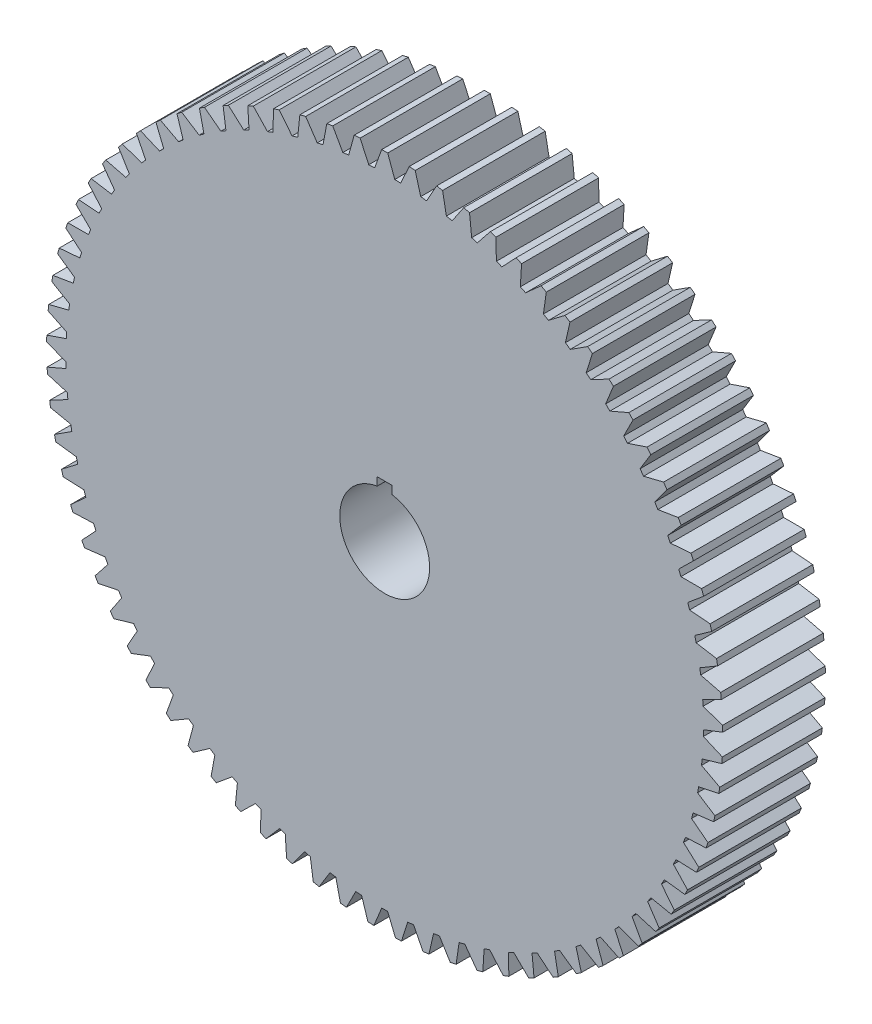
SolidWorks part; units mm, degrees
ref_plane "Front Plane" through (0, 0, 0) normal (0, 0, 1) x (1, 0, 0)
ref_plane "Top Plane" through (0, 0, 0) normal (0, 1, 0) x (1, 0, 0)
ref_plane "Right Plane" through (0, 0, 0) normal (1, 0, 0) x (0, 0, -1)
sketch "Sketch2" plane through (0, 0, 0) normal (0, 0, 1) x (1, 0, 0)
  line L0 (1.27, 143.3266) -> (4.2647, 135.0988)
  line L1 (-1.27, 143.3266) -> (-4.2647, 135.0988)
  line L2 (0, 19.05) -> (0, 143.3322) construction
  line L3 (12.9482, 142.7461) -> (15.2623, 134.3017)
  line L4 (10.4167, 142.9532) -> (6.7613, 134.9969)
  line L5 (24.5403, 141.2158) -> (26.1583, 132.6108)
  line L6 (22.034, 141.6285) -> (17.7423, 133.9966)
  line L7 (35.969, 138.7456) -> (36.8803, 130.0374)
  line L8 (33.5047, 139.3612) -> (28.6053, 132.1046)
  line L9 (47.1584, 135.3522) -> (47.3568, 126.5986)
  line L10 (44.7525, 136.1666) -> (39.2778, 129.3334)
  line L11 (58.0339, 131.0579) -> (57.5182, 122.3173)
  line L12 (55.7024, 132.0657) -> (49.689, 125.7015)
  line L13 (68.5233, 125.8915) -> (67.2968, 117.2221)
  line L14 (66.2817, 127.086) -> (59.7695, 121.2332)
  line L15 (78.5566, 119.8874) -> (76.6276, 111.3467)
  line L16 (76.4198, 121.2606) -> (69.4523, 115.958)
  line L17 (88.0671, 113.0854) -> (85.4484, 104.7303)
  line L18 (86.0494, 114.6282) -> (78.6728, 109.9112)
  line L19 (96.9916, 105.5308) -> (93.7006, 97.417)
  line L20 (95.1063, 107.233) -> (87.3698, 103.1329)
  line L21 (105.2706, 97.2739) -> (101.3292, 89.4554)
  line L22 (103.5304, 99.1241) -> (95.4854, 95.6682)
  line L23 (112.8491, 88.3697) -> (108.2835, 80.8985)
  line L24 (111.2654, 90.3556) -> (102.9655, 87.567)
  line L25 (119.6765, 78.8774) -> (114.5171, 71.8032)
  line L26 (118.26, 80.9858) -> (109.7604, 78.883)
  line L27 (125.7075, 68.8602) -> (119.9887, 62.2301)
  line L28 (124.4676, 71.077) -> (115.8249, 69.674)
  line L29 (130.902, 58.3848) -> (124.6618, 52.2428)
  line L30 (129.8469, 60.6952) -> (121.1186, 60.0013)
  line L31 (135.2253, 47.5208) -> (128.5053, 41.9079)
  line L32 (134.362, 49.9096) -> (125.6062, 49.9294)
  line L33 (138.6488, 36.3405) -> (131.4936, 31.2941)
  line L34 (137.983, 38.7917) -> (129.258, 39.5252)
  line L35 (141.1495, 24.9185) -> (133.6068, 20.472)
  line L36 (140.6858, 27.4158) -> (132.0496, 28.858)
  line L37 (142.711, 13.3305) -> (134.8309, 9.5137)
  line L38 (142.4523, 15.8573) -> (133.9624, 17.9987)
  line L39 (143.3227, 1.6539) -> (135.1577, -1.508)
  line L40 (143.2708, 4.1934) -> (134.9837, 7.0196)
  line L41 (142.9806, -10.0337) -> (134.585, -12.5195)
  line L42 (143.1359, -7.4985) -> (135.1067, -4.0062)
  line L43 (141.687, -21.6546) -> (133.1168, -23.4478)
  line L44 (142.0485, -19.1404) -> (134.3306, -15.0053)
  line L45 (139.4505, -33.1313) -> (130.7626, -34.2201)
  line L46 (140.0157, -30.655) -> (132.6606, -25.9046)
  line L47 (136.286, -44.3876) -> (127.5383, -44.7646)
  line L48 (137.0511, -41.9656) -> (130.1077, -36.6314)
  line L49 (132.2145, -55.3485) -> (123.4652, -55.0112)
  line L50 (133.1745, -52.9969) -> (126.689, -47.1145)
  line L51 (127.2631, -65.941) -> (118.5704, -64.8917)
  line L52 (128.4116, -63.6755) -> (122.4271, -57.2841)
  line L53 (121.4649, -76.0947) -> (112.8866, -74.3403)
  line L54 (122.7942, -73.9304) -> (117.3506, -67.0724)
  line L55 (114.8583, -85.742) -> (106.4516, -83.2943)
  line L56 (116.3596, -83.6932) -> (111.4931, -76.4144)
  line L57 (107.4873, -94.8187) -> (99.3081, -91.6939)
  line L58 (109.1507, -92.8991) -> (104.8936, -85.2479)
  line L59 (99.4011, -103.2645) -> (91.5038, -99.4833)
  line L60 (101.2153, -101.4868) -> (97.5961, -93.514)
  line L61 (90.6533, -111.023) -> (83.0905, -106.6107)
  line L62 (92.6064, -109.3991) -> (89.6491, -101.1579)
  line L63 (81.3023, -118.0426) -> (74.1242, -113.0286)
  line L64 (83.3812, -116.5834) -> (81.1055, -108.1285)
  line L65 (71.4102, -124.2767) -> (64.6647, -118.6944)
  line L66 (73.6012, -122.9918) -> (72.0221, -114.3796)
  line L67 (61.0428, -129.6838) -> (54.7748, -123.5702)
  line L68 (63.3313, -128.5817) -> (62.4595, -119.8695)
  line L69 (50.2693, -134.2279) -> (44.5205, -127.6237)
  line L70 (52.64, -133.316) -> (52.4812, -124.5616)
  line L71 (39.1612, -137.8786) -> (33.9698, -130.8278)
  line L72 (41.5983, -137.163) -> (42.1536, -128.4249)
  line L73 (27.7925, -140.6119) -> (23.1931, -133.1614)
  line L74 (30.2798, -140.0973) -> (31.5456, -131.4335)
  line L75 (16.2389, -142.4093) -> (12.262, -134.6088)
  line L76 (18.7599, -142.0992) -> (20.7276, -133.5674)
  line L77 (4.5771, -143.2591) -> (1.2494, -135.1603)
  line L78 (7.115, -143.1555) -> (9.7716, -134.8124)
  line L79 (-7.115, -143.1555) -> (-9.7716, -134.8124)
  line L80 (-4.5771, -143.2591) -> (-1.2494, -135.1603)
  line L81 (-18.7599, -142.0992) -> (-20.7276, -133.5674)
  line L82 (-16.2389, -142.4093) -> (-12.262, -134.6088)
  line L83 (-30.2798, -140.0973) -> (-31.5456, -131.4335)
  line L84 (-27.7925, -140.6119) -> (-23.1931, -133.1614)
  line L85 (-41.5983, -137.163) -> (-42.1536, -128.4249)
  line L86 (-39.1612, -137.8786) -> (-33.9698, -130.8278)
  line L87 (-52.64, -133.316) -> (-52.4812, -124.5616)
  line L88 (-50.2693, -134.2279) -> (-44.5205, -127.6237)
  line L89 (-63.3313, -128.5817) -> (-62.4595, -119.8695)
  line L90 (-61.0428, -129.6838) -> (-54.7748, -123.5702)
  line L91 (-73.6012, -122.9918) -> (-72.0221, -114.3796)
  line L92 (-71.4102, -124.2767) -> (-64.6647, -118.6944)
  line L93 (-83.3812, -116.5834) -> (-81.1055, -108.1285)
  line L94 (-81.3023, -118.0426) -> (-74.1242, -113.0286)
  line L95 (-92.6064, -109.3991) -> (-89.6491, -101.1579)
  line L96 (-90.6533, -111.023) -> (-83.0905, -106.6107)
  line L97 (-101.2153, -101.4868) -> (-97.5961, -93.514)
  line L98 (-99.4011, -103.2645) -> (-91.5038, -99.4833)
  line L99 (-109.1507, -92.8991) -> (-104.8936, -85.2479)
  line L100 (-107.4873, -94.8187) -> (-99.3081, -91.6939)
  line L101 (-116.3596, -83.6932) -> (-111.4931, -76.4144)
  line L102 (-114.8583, -85.742) -> (-106.4516, -83.2943)
  line L103 (-122.7942, -73.9304) -> (-117.3506, -67.0724)
  line L104 (-121.4649, -76.0947) -> (-112.8866, -74.3403)
  line L105 (-128.4116, -63.6755) -> (-122.4271, -57.2841)
  line L106 (-127.2631, -65.941) -> (-118.5704, -64.8917)
  line L107 (-133.1745, -52.9969) -> (-126.689, -47.1145)
  line L108 (-132.2145, -55.3485) -> (-123.4652, -55.0112)
  line L109 (-137.0511, -41.9656) -> (-130.1077, -36.6314)
  line L110 (-136.286, -44.3876) -> (-127.5383, -44.7646)
  line L111 (-140.0157, -30.655) -> (-132.6606, -25.9046)
  line L112 (-139.4505, -33.1313) -> (-130.7626, -34.2201)
  line L113 (-142.0485, -19.1404) -> (-134.3306, -15.0053)
  line L114 (-141.687, -21.6546) -> (-133.1168, -23.4478)
  line L115 (-143.1359, -7.4985) -> (-135.1067, -4.0062)
  line L116 (-142.9806, -10.0337) -> (-134.585, -12.5195)
  line L117 (-143.2708, 4.1934) -> (-134.9837, 7.0196)
  line L118 (-143.3227, 1.6539) -> (-135.1577, -1.508)
  line L119 (-142.4523, 15.8573) -> (-133.9624, 17.9987)
  line L120 (-142.711, 13.3305) -> (-134.8309, 9.5137)
  line L121 (-140.6858, 27.4158) -> (-132.0496, 28.858)
  line L122 (-141.1495, 24.9185) -> (-133.6068, 20.472)
  line L123 (-137.983, 38.7917) -> (-129.258, 39.5252)
  line L124 (-138.6488, 36.3405) -> (-131.4936, 31.2941)
  line L125 (-134.362, 49.9096) -> (-125.6062, 49.9294)
  line L126 (-135.2253, 47.5208) -> (-128.5053, 41.9079)
  line L127 (-129.8469, 60.6952) -> (-121.1186, 60.0013)
  line L128 (-130.902, 58.3848) -> (-124.6618, 52.2428)
  line L129 (-124.4676, 71.077) -> (-115.8249, 69.674)
  line L130 (-125.7075, 68.8602) -> (-119.9887, 62.2301)
  line L131 (-118.26, 80.9858) -> (-109.7604, 78.883)
  line L132 (-119.6765, 78.8774) -> (-114.5171, 71.8032)
  line L133 (-111.2654, 90.3556) -> (-102.9655, 87.567)
  line L134 (-112.8491, 88.3697) -> (-108.2835, 80.8985)
  line L135 (-103.5304, 99.1241) -> (-95.4854, 95.6682)
  line L136 (-105.2706, 97.2739) -> (-101.3292, 89.4554)
  line L137 (-95.1063, 107.233) -> (-87.3698, 103.1329)
  line L138 (-96.9916, 105.5308) -> (-93.7006, 97.417)
  line L139 (-86.0494, 114.6282) -> (-78.6728, 109.9112)
  line L140 (-88.0671, 113.0854) -> (-85.4484, 104.7303)
  line L141 (-76.4198, 121.2606) -> (-69.4523, 115.958)
  line L142 (-78.5566, 119.8874) -> (-76.6276, 111.3467)
  line L143 (-66.2817, 127.086) -> (-59.7695, 121.2332)
  line L144 (-68.5233, 125.8915) -> (-67.2968, 117.2221)
  line L145 (-55.7024, 132.0657) -> (-49.689, 125.7015)
  line L146 (-58.0339, 131.0579) -> (-57.5182, 122.3173)
  line L147 (-44.7525, 136.1666) -> (-39.2778, 129.3334)
  line L148 (-47.1584, 135.3522) -> (-47.3568, 126.5986)
  line L149 (-33.5047, 139.3612) -> (-28.6053, 132.1046)
  line L150 (-35.969, 138.7456) -> (-36.8803, 130.0374)
  line L151 (-22.034, 141.6285) -> (-17.7423, 133.9966)
  line L152 (-24.5403, 141.2158) -> (-26.1583, 132.6108)
  line L153 (-10.4167, 142.9532) -> (-6.7613, 134.9969)
  line L154 (-12.9482, 142.7461) -> (-15.2623, 134.3017)
  line L156 (0, 22.225) -> (-3.175, 22.225)
  line L157 (-3.175, 22.225) -> (-3.175, 18.7836)
  line L158 (0, 22.225) -> (3.175, 22.225)
  line L159 (3.175, 22.225) -> (3.175, 18.7836)
  arc A1 (1.27, 143.3266) -> (-1.27, 143.3266) centre (0, 0) ccw
  arc A3 (12.9482, 142.7461) -> (10.4167, 142.9532) centre (0, 0) ccw
  arc A5 (24.5403, 141.2158) -> (22.034, 141.6285) centre (0, 0) ccw
  arc A7 (35.969, 138.7456) -> (33.5047, 139.3612) centre (0, 0) ccw
  arc A9 (47.1584, 135.3522) -> (44.7525, 136.1666) centre (0, 0) ccw
  arc A11 (58.0339, 131.0579) -> (55.7024, 132.0657) centre (0, 0) ccw
  arc A13 (68.5233, 125.8915) -> (66.2817, 127.086) centre (0, 0) ccw
  arc A15 (78.5566, 119.8874) -> (76.4198, 121.2606) centre (0, 0) ccw
  arc A17 (88.0671, 113.0854) -> (86.0494, 114.6282) centre (0, 0) ccw
  arc A19 (96.9916, 105.5308) -> (95.1063, 107.233) centre (0, 0) ccw
  arc A21 (105.2706, 97.2739) -> (103.5304, 99.1241) centre (0, 0) ccw
  arc A23 (112.8491, 88.3697) -> (111.2654, 90.3556) centre (0, 0) ccw
  arc A25 (119.6765, 78.8774) -> (118.26, 80.9858) centre (0, 0) ccw
  arc A27 (125.7075, 68.8602) -> (124.4676, 71.077) centre (0, 0) ccw
  arc A29 (130.902, 58.3848) -> (129.8469, 60.6952) centre (0, 0) ccw
  arc A31 (135.2253, 47.5208) -> (134.362, 49.9096) centre (0, 0) ccw
  arc A33 (138.6488, 36.3405) -> (137.983, 38.7917) centre (0, 0) ccw
  arc A35 (141.1495, 24.9185) -> (140.6858, 27.4158) centre (0, 0) ccw
  arc A37 (142.711, 13.3305) -> (142.4523, 15.8573) centre (0, 0) ccw
  arc A39 (143.3227, 1.6539) -> (143.2708, 4.1934) centre (0, 0) ccw
  arc A41 (142.9806, -10.0337) -> (143.1359, -7.4985) centre (0, 0) ccw
  arc A43 (141.687, -21.6546) -> (142.0485, -19.1404) centre (0, 0) ccw
  arc A45 (139.4505, -33.1313) -> (140.0157, -30.655) centre (0, 0) ccw
  arc A47 (136.286, -44.3876) -> (137.0511, -41.9656) centre (0, 0) ccw
  arc A49 (132.2145, -55.3485) -> (133.1745, -52.9969) centre (0, 0) ccw
  arc A51 (127.2631, -65.941) -> (128.4116, -63.6755) centre (0, 0) ccw
  arc A53 (121.4649, -76.0947) -> (122.7942, -73.9304) centre (0, 0) ccw
  arc A55 (114.8583, -85.742) -> (116.3596, -83.6932) centre (0, 0) ccw
  arc A57 (107.4873, -94.8187) -> (109.1507, -92.8991) centre (0, 0) ccw
  arc A59 (99.4011, -103.2645) -> (101.2153, -101.4868) centre (0, 0) ccw
  arc A61 (90.6533, -111.023) -> (92.6064, -109.3991) centre (0, 0) ccw
  arc A63 (81.3023, -118.0426) -> (83.3812, -116.5834) centre (0, 0) ccw
  arc A65 (71.4102, -124.2767) -> (73.6012, -122.9918) centre (0, 0) ccw
  arc A67 (61.0428, -129.6838) -> (63.3313, -128.5817) centre (0, 0) ccw
  arc A69 (50.2693, -134.2279) -> (52.64, -133.316) centre (0, 0) ccw
  arc A71 (39.1612, -137.8786) -> (41.5983, -137.163) centre (0, 0) ccw
  arc A73 (27.7925, -140.6119) -> (30.2798, -140.0973) centre (0, 0) ccw
  arc A75 (16.2389, -142.4093) -> (18.7599, -142.0992) centre (0, 0) ccw
  arc A77 (4.5771, -143.2591) -> (7.115, -143.1555) centre (0, 0) ccw
  arc A79 (-7.115, -143.1555) -> (-4.5771, -143.2591) centre (0, 0) ccw
  arc A81 (-18.7599, -142.0992) -> (-16.2389, -142.4093) centre (0, 0) ccw
  arc A83 (-30.2798, -140.0973) -> (-27.7925, -140.6119) centre (0, 0) ccw
  arc A85 (-41.5983, -137.163) -> (-39.1612, -137.8786) centre (0, 0) ccw
  arc A87 (-52.64, -133.316) -> (-50.2693, -134.2279) centre (0, 0) ccw
  arc A89 (-63.3313, -128.5817) -> (-61.0428, -129.6838) centre (0, 0) ccw
  arc A91 (-73.6012, -122.9918) -> (-71.4102, -124.2767) centre (0, 0) ccw
  arc A93 (-83.3812, -116.5834) -> (-81.3023, -118.0426) centre (0, 0) ccw
  arc A95 (-92.6064, -109.3991) -> (-90.6533, -111.023) centre (0, 0) ccw
  arc A97 (-101.2153, -101.4868) -> (-99.4011, -103.2645) centre (0, 0) ccw
  arc A99 (-109.1507, -92.8991) -> (-107.4873, -94.8187) centre (0, 0) ccw
  arc A101 (-116.3596, -83.6932) -> (-114.8583, -85.742) centre (0, 0) ccw
  arc A103 (-122.7942, -73.9304) -> (-121.4649, -76.0947) centre (0, 0) ccw
  arc A105 (-128.4116, -63.6755) -> (-127.2631, -65.941) centre (0, 0) ccw
  arc A107 (-133.1745, -52.9969) -> (-132.2145, -55.3485) centre (0, 0) ccw
  arc A109 (-137.0511, -41.9656) -> (-136.286, -44.3876) centre (0, 0) ccw
  arc A111 (-140.0157, -30.655) -> (-139.4505, -33.1313) centre (0, 0) ccw
  arc A113 (-142.0485, -19.1404) -> (-141.687, -21.6546) centre (0, 0) ccw
  arc A115 (-143.1359, -7.4985) -> (-142.9806, -10.0337) centre (0, 0) ccw
  arc A117 (-143.2708, 4.1934) -> (-143.3227, 1.6539) centre (0, 0) ccw
  arc A119 (-142.4523, 15.8573) -> (-142.711, 13.3305) centre (0, 0) ccw
  arc A121 (-140.6858, 27.4158) -> (-141.1495, 24.9185) centre (0, 0) ccw
  arc A123 (-137.983, 38.7917) -> (-138.6488, 36.3405) centre (0, 0) ccw
  arc A125 (-134.362, 49.9096) -> (-135.2253, 47.5208) centre (0, 0) ccw
  arc A127 (-129.8469, 60.6952) -> (-130.902, 58.3848) centre (0, 0) ccw
  arc A129 (-124.4676, 71.077) -> (-125.7075, 68.8602) centre (0, 0) ccw
  arc A131 (-118.26, 80.9858) -> (-119.6765, 78.8774) centre (0, 0) ccw
  arc A133 (-111.2654, 90.3556) -> (-112.8491, 88.3697) centre (0, 0) ccw
  arc A135 (-103.5304, 99.1241) -> (-105.2706, 97.2739) centre (0, 0) ccw
  arc A137 (-95.1063, 107.233) -> (-96.9916, 105.5308) centre (0, 0) ccw
  arc A139 (-86.0494, 114.6282) -> (-88.0671, 113.0854) centre (0, 0) ccw
  arc A141 (-76.4198, 121.2606) -> (-78.5566, 119.8874) centre (0, 0) ccw
  arc A143 (-66.2817, 127.086) -> (-68.5233, 125.8915) centre (0, 0) ccw
  arc A145 (-55.7024, 132.0657) -> (-58.0339, 131.0579) centre (0, 0) ccw
  arc A147 (-44.7525, 136.1666) -> (-47.1584, 135.3522) centre (0, 0) ccw
  arc A149 (-33.5047, 139.3612) -> (-35.969, 138.7456) centre (0, 0) ccw
  arc A151 (-22.034, 141.6285) -> (-24.5403, 141.2158) centre (0, 0) ccw
  arc A153 (-10.4167, 142.9532) -> (-12.9482, 142.7461) centre (0, 0) ccw
  arc A154 (-26.1583, 132.6108) -> (-28.6053, 132.1046) centre (0, 0) ccw
  arc A155 (-3.175, 18.7836) -> (3.175, 18.7836) centre (0, 0) ccw
  arc A156 (-15.2623, 134.3017) -> (-17.7423, 133.9966) centre (0, 0) ccw
  arc A158 (-4.2647, 135.0988) -> (-6.7613, 134.9969) centre (0, 0) ccw
  arc A159 (6.7613, 134.9969) -> (4.2647, 135.0988) centre (0, 0) ccw
  arc A160 (17.7423, 133.9966) -> (15.2623, 134.3017) centre (0, 0) ccw
  arc A161 (28.6053, 132.1046) -> (26.1583, 132.6108) centre (0, 0) ccw
  arc A162 (39.2778, 129.3334) -> (36.8803, 130.0374) centre (0, 0) ccw
  arc A163 (49.689, 125.7015) -> (47.3568, 126.5986) centre (0, 0) ccw
  arc A164 (59.7695, 121.2332) -> (57.5182, 122.3173) centre (0, 0) ccw
  arc A165 (69.4523, 115.958) -> (67.2968, 117.2221) centre (0, 0) ccw
  arc A166 (78.6728, 109.9112) -> (76.6276, 111.3467) centre (0, 0) ccw
  arc A167 (87.3698, 103.1329) -> (85.4484, 104.7303) centre (0, 0) ccw
  arc A168 (95.4854, 95.6682) -> (93.7006, 97.417) centre (0, 0) ccw
  arc A169 (102.9655, 87.567) -> (101.3292, 89.4554) centre (0, 0) ccw
  arc A170 (109.7604, 78.883) -> (108.2835, 80.8985) centre (0, 0) ccw
  arc A171 (115.8249, 69.674) -> (114.5171, 71.8032) centre (0, 0) ccw
  arc A172 (121.1186, 60.0013) -> (119.9887, 62.2301) centre (0, 0) ccw
  arc A173 (125.6062, 49.9294) -> (124.6618, 52.2428) centre (0, 0) ccw
  arc A174 (129.258, 39.5252) -> (128.5053, 41.9079) centre (0, 0) ccw
  arc A175 (132.0496, 28.858) -> (131.4936, 31.2941) centre (0, 0) ccw
  arc A176 (133.9624, 17.9987) -> (133.6068, 20.472) centre (0, 0) ccw
  arc A177 (134.9837, 7.0196) -> (134.8309, 9.5137) centre (0, 0) ccw
  arc A178 (135.1067, -4.0062) -> (135.1577, -1.508) centre (0, 0) ccw
  arc A179 (134.3306, -15.0053) -> (134.585, -12.5195) centre (0, 0) ccw
  arc A180 (132.6606, -25.9046) -> (133.1168, -23.4478) centre (0, 0) ccw
  arc A181 (130.1077, -36.6314) -> (130.7626, -34.2201) centre (0, 0) ccw
  arc A182 (126.689, -47.1145) -> (127.5383, -44.7646) centre (0, 0) ccw
  arc A183 (122.4271, -57.2841) -> (123.4652, -55.0112) centre (0, 0) ccw
  arc A184 (117.3506, -67.0724) -> (118.5704, -64.8917) centre (0, 0) ccw
  arc A185 (111.4931, -76.4144) -> (112.8866, -74.3403) centre (0, 0) ccw
  arc A186 (104.8936, -85.2479) -> (106.4516, -83.2943) centre (0, 0) ccw
  arc A187 (97.5961, -93.514) -> (99.3081, -91.6939) centre (0, 0) ccw
  arc A188 (89.6491, -101.1579) -> (91.5038, -99.4833) centre (0, 0) ccw
  arc A189 (81.1055, -108.1285) -> (83.0905, -106.6107) centre (0, 0) ccw
  arc A190 (72.0221, -114.3796) -> (74.1242, -113.0286) centre (0, 0) ccw
  arc A191 (62.4595, -119.8695) -> (64.6647, -118.6944) centre (0, 0) ccw
  arc A192 (52.4812, -124.5616) -> (54.7748, -123.5702) centre (0, 0) ccw
  arc A193 (42.1536, -128.4249) -> (44.5205, -127.6237) centre (0, 0) ccw
  arc A194 (31.5456, -131.4335) -> (33.9698, -130.8278) centre (0, 0) ccw
  arc A195 (20.7276, -133.5674) -> (23.1931, -133.1614) centre (0, 0) ccw
  arc A196 (9.7716, -134.8124) -> (12.262, -134.6088) centre (0, 0) ccw
  arc A197 (-1.2494, -135.1603) -> (1.2494, -135.1603) centre (0, 0) ccw
  arc A198 (-12.262, -134.6088) -> (-9.7716, -134.8124) centre (0, 0) ccw
  arc A199 (-23.1931, -133.1614) -> (-20.7276, -133.5674) centre (0, 0) ccw
  arc A200 (-33.9698, -130.8278) -> (-31.5456, -131.4335) centre (0, 0) ccw
  arc A201 (-44.5205, -127.6237) -> (-42.1536, -128.4249) centre (0, 0) ccw
  arc A202 (-54.7748, -123.5702) -> (-52.4812, -124.5616) centre (0, 0) ccw
  arc A203 (-64.6647, -118.6944) -> (-62.4595, -119.8695) centre (0, 0) ccw
  arc A204 (-74.1242, -113.0286) -> (-72.0221, -114.3796) centre (0, 0) ccw
  arc A205 (-83.0905, -106.6107) -> (-81.1055, -108.1285) centre (0, 0) ccw
  arc A206 (-91.5038, -99.4833) -> (-89.6491, -101.1579) centre (0, 0) ccw
  arc A207 (-99.3081, -91.6939) -> (-97.5961, -93.514) centre (0, 0) ccw
  arc A208 (-112.8866, -74.3403) -> (-111.4931, -76.4144) centre (0, 0) ccw
  arc A209 (-106.4516, -83.2943) -> (-104.8936, -85.2479) centre (0, 0) ccw
  arc A210 (-118.5704, -64.8917) -> (-117.3506, -67.0724) centre (0, 0) ccw
  arc A211 (-123.4652, -55.0112) -> (-122.4271, -57.2841) centre (0, 0) ccw
  arc A212 (-127.5383, -44.7646) -> (-126.689, -47.1145) centre (0, 0) ccw
  arc A213 (-130.7626, -34.2201) -> (-130.1077, -36.6314) centre (0, 0) ccw
  arc A214 (-133.1168, -23.4478) -> (-132.6606, -25.9046) centre (0, 0) ccw
  arc A215 (-134.585, -12.5195) -> (-134.3306, -15.0053) centre (0, 0) ccw
  arc A216 (-135.1577, -1.508) -> (-135.1067, -4.0062) centre (0, 0) ccw
  arc A217 (-134.8309, 9.5137) -> (-134.9837, 7.0196) centre (0, 0) ccw
  arc A218 (-133.6068, 20.472) -> (-133.9624, 17.9987) centre (0, 0) ccw
  arc A219 (-131.4936, 31.2941) -> (-132.0496, 28.858) centre (0, 0) ccw
  arc A220 (-128.5053, 41.9079) -> (-129.258, 39.5252) centre (0, 0) ccw
  arc A221 (-124.6618, 52.2428) -> (-125.6062, 49.9294) centre (0, 0) ccw
  arc A222 (-119.9887, 62.2301) -> (-121.1186, 60.0013) centre (0, 0) ccw
  arc A223 (-114.5171, 71.8032) -> (-115.8249, 69.674) centre (0, 0) ccw
  arc A224 (-108.2835, 80.8985) -> (-109.7604, 78.883) centre (0, 0) ccw
  arc A225 (-101.3292, 89.4554) -> (-102.9655, 87.567) centre (0, 0) ccw
  arc A226 (-93.7006, 97.417) -> (-95.4854, 95.6682) centre (0, 0) ccw
  arc A227 (-85.4484, 104.7303) -> (-87.3698, 103.1329) centre (0, 0) ccw
  arc A228 (-76.6276, 111.3467) -> (-78.6728, 109.9112) centre (0, 0) ccw
  arc A229 (-67.2968, 117.2221) -> (-69.4523, 115.958) centre (0, 0) ccw
  arc A230 (-57.5182, 122.3173) -> (-59.7695, 121.2332) centre (0, 0) ccw
  arc A231 (-47.3568, 126.5986) -> (-49.689, 125.7015) centre (0, 0) ccw
  arc A232 (-36.8803, 130.0374) -> (-39.2778, 129.3334) centre (0, 0) ccw
  point P314 (0, 0)
  dimension "D1" = 38.1
  dimension "D2" = 286.6644
  dimension "D3" = 20
  dimension "D4" = 20
  dimension "D5" = 1.27
  dimension "D6" = 1.27
  dimension "D8" = 22.225
  dimension "D9" = 3.175
  dimension "D10" = 3.175
  dimension "D7" = 77
extrude "Boss-Extrude1" add sketch "Sketch2" along normal blind 43.5102
